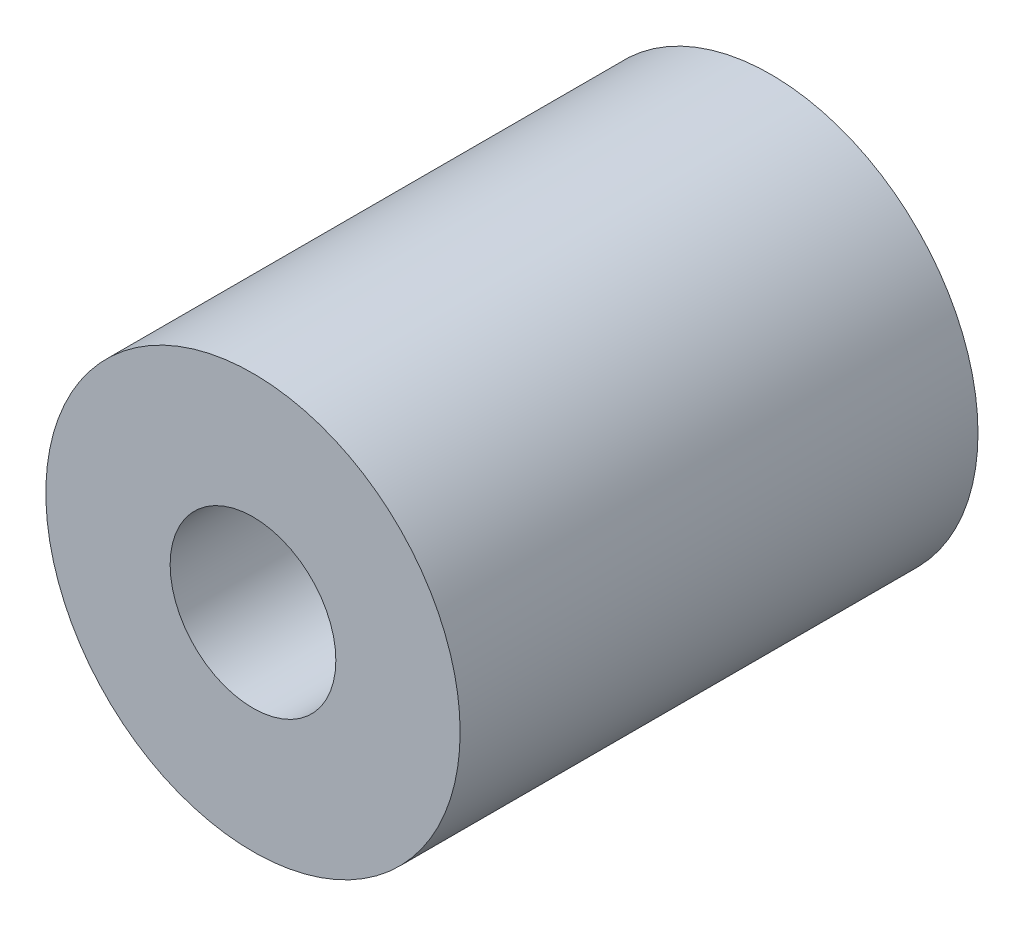
SolidWorks part; units mm, degrees
ref_plane "Front Plane" through (0, 0, 0) normal (0, 0, 1) x (1, 0, 0)
ref_plane "Top Plane" through (0, 0, 0) normal (0, 1, 0) x (1, 0, 0)
ref_plane "Right Plane" through (0, 0, 0) normal (1, 0, 0) x (0, 0, -1)
sketch "Sketch1" plane through (0, 0, 0) normal (0, 0, 1) x (1, 0, 0)
  line L0 (0, 1.6) -> (0, 4) construction
  line L1 (0, -1.6) -> (0, -4) construction
  circle A0 centre (0, 0) radius 4
  circle A1 centre (0, 0) radius 1.6
  dimension "OD" = 8
  dimension "ID" = 3.2
sketch "Sketch2" plane through (0, 0, 0) normal (1, 0, 0) x (0, 0, -1)
  line L0 (-5, 1.6) -> (5, 1.6) construction
  line L1 (-5, -1.6) -> (5, -1.6) construction
  line L2 (-5, -4) -> (5, -4) construction
  line L3 (-5, 4) -> (5, 4) construction
  dimension "Length" = 10
extrude "Extrude1" add sketch "Sketch1" along normal up to vertex (5 mm away) and the other way up to vertex (5 mm away) up to point (0, 1.6, 5) other way up to point (0, 1.6, -5)
sketch "Sketch3" plane through (0, 0, 5) normal (0, 0, 1) x (1, 0, 0)
  circle A0 centre (0, 0) radius 1.6 construction
  circle A3 centre (0, 0) radius 1.6
  point P3 (-1.6, 0)
